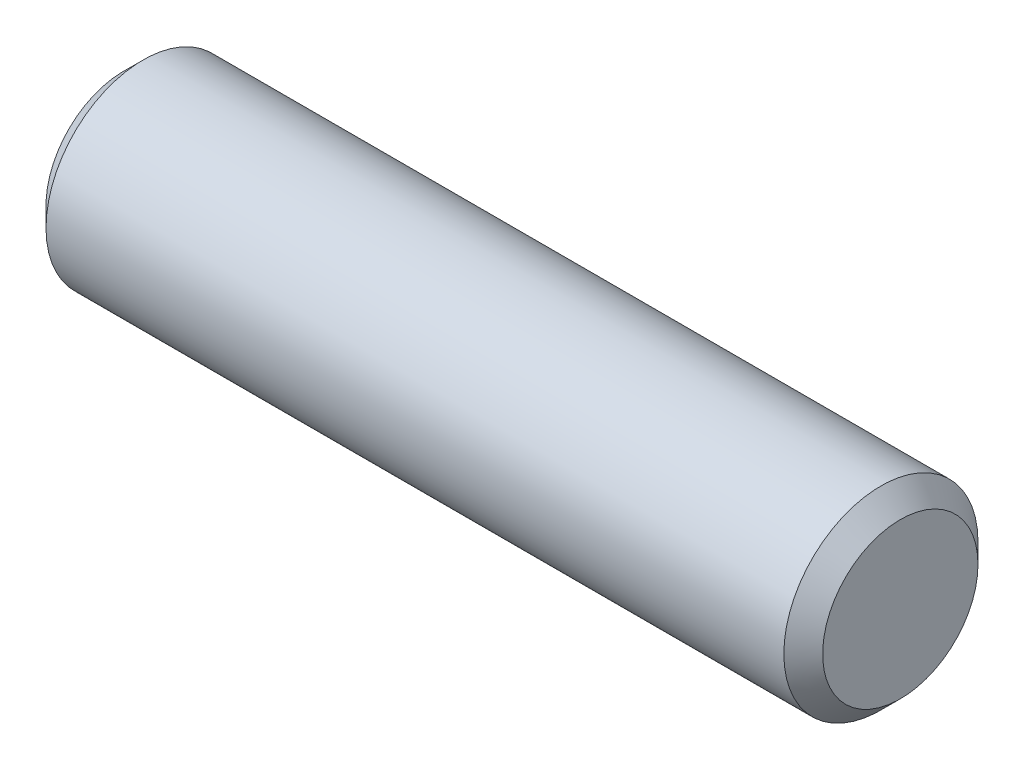
SolidWorks part; units mm, degrees
ref_plane "Front Plane" through (0, 0, 0) normal (0, 0, 1) x (1, 0, 0)
ref_plane "Top Plane" through (0, 0, 0) normal (0, 1, 0) x (1, 0, 0)
ref_plane "Right Plane" through (0, 0, 0) normal (1, 0, 0) x (0, 0, -1)
sketch "Sketch1" plane through (0, 0, 0) normal (0, 0, 1) x (1, 0, 0)
  line L0 (-6.35, 0) -> (6.35, 0) construction
  line L1 (-6.35, 1.5875) -> (-6.35, -1.5875) construction
  line L2 (6.35, 1.5875) -> (6.35, -1.5875) construction
  dimension "Diameter" = 3.175
  dimension "Length" = 12.7
sketch "Sketch2" plane through (0, 0, 0) normal (1, 0, 0) x (0, 0, -1)
  circle A0 centre (0, 0) radius 1.5875
extrude "Extrude1" add sketch "Sketch2" against normal up to vertex (6.35 mm away) and the other way up to vertex (6.35 mm away) up to point (-6.35, 0, 0) other way up to point (6.35, 0, 0)
chamfer "Chamfer1" distance 0.3175 angle 45 2 edges at (6.35, 0, -1.5875) (-6.35, 0, -1.5875)
equation "\"D1@Chamfer1\" = \"Diameter@Sketch1\"*.1"
